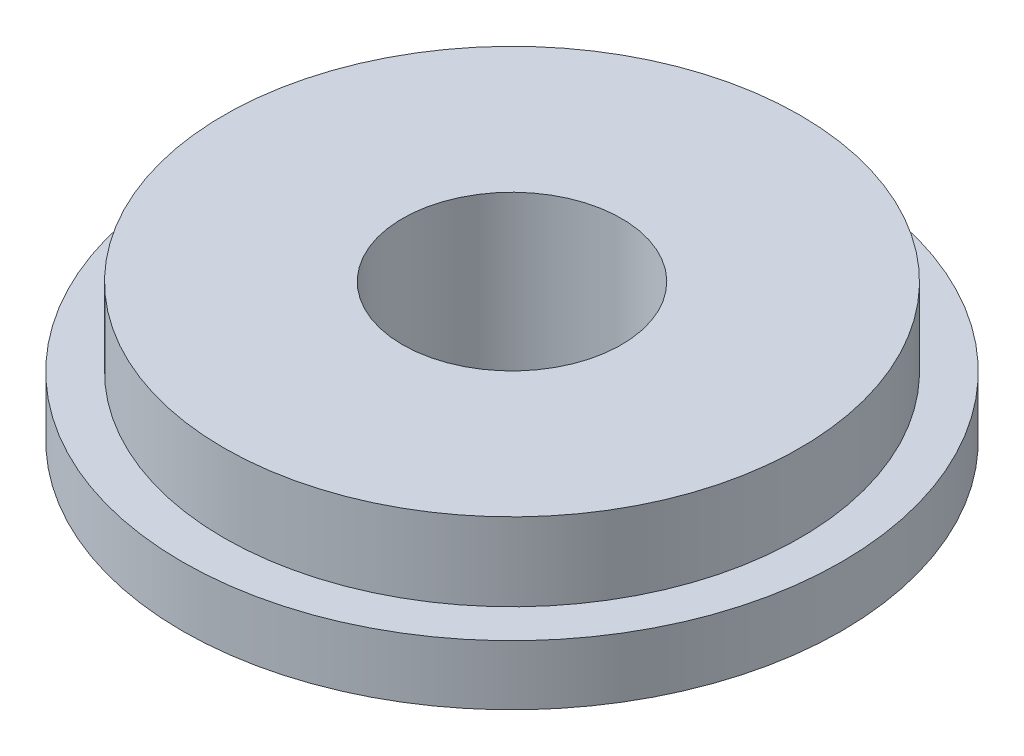
SolidWorks part; units mm, degrees
material "Plain Carbon Steel"
ref_plane "Front Plane" through (0, 0, 0) normal (0, 0, 1) x (1, 0, 0)
ref_plane "Top Plane" through (0, 0, 0) normal (0, 1, 0) x (1, 0, 0)
ref_plane "Right Plane" through (0, 0, 0) normal (1, 0, 0) x (0, 0, -1)
sketch "Sketch1" plane through (0, 0, 0) normal (0, 1, 0) x (1, 0, 0)
  circle A0 centre (0, 0) radius 12.7
  dimension "D1" = 25.4
extrude "Extrude1" add sketch "Sketch1" along normal blind 9
sketch "Sketch2" plane through (0, 0, 0) normal (0, 1, 0) x (1, 0, 0)
  circle A0 centre (0, 0) radius 4.2164
  dimension "D1" = 8.4328
extrude "Extrude2" cut sketch "Sketch2" along normal blind 25.4
cosmetic thread "Cosmetic Thread1" parameters "D2"=9.525
sketch "Sketch3" plane through (0, 9, 0) normal (0, 1, 0) x (1, 0, 0)
  circle A0 centre (0, 0) radius 11.1
  circle A1 centre (0, 0) radius 12.7 construction
  dimension "D1" = 1.6
extrude "Extrude3" cut sketch "Sketch3" against normal blind 3 flip side to cut
sketch "Sketch5" plane through (0, 0, 0) normal (1, 0, 0) x (0, 0, -1)
  line L0 (0, 45.7263) -> (0, -5.8121) construction
sketch "Sketch6" plane through (0, 0, 0) normal (1, 0, 0) x (0, 0, -1)
  line L0 (-1.1038, -3) -> (-15, 5.0229)
  line L1 (-15, 5.0229) -> (-15, -3)
  line L2 (-15, -3) -> (-1.1038, -3)
  line L3 (-12.7, 0) -> (12.7, 0) construction
  line L4 (0, 0) -> (0, -6.3345) construction
  point P2 (-6.3, 0)
  dimension "D1" = 30
  dimension "D2" = 3
  dimension "D3" = 15
  dimension "D4" = 12.6
revolve "Cut-Revolve1" cut sketch "Sketch6" angle 360 about L4
